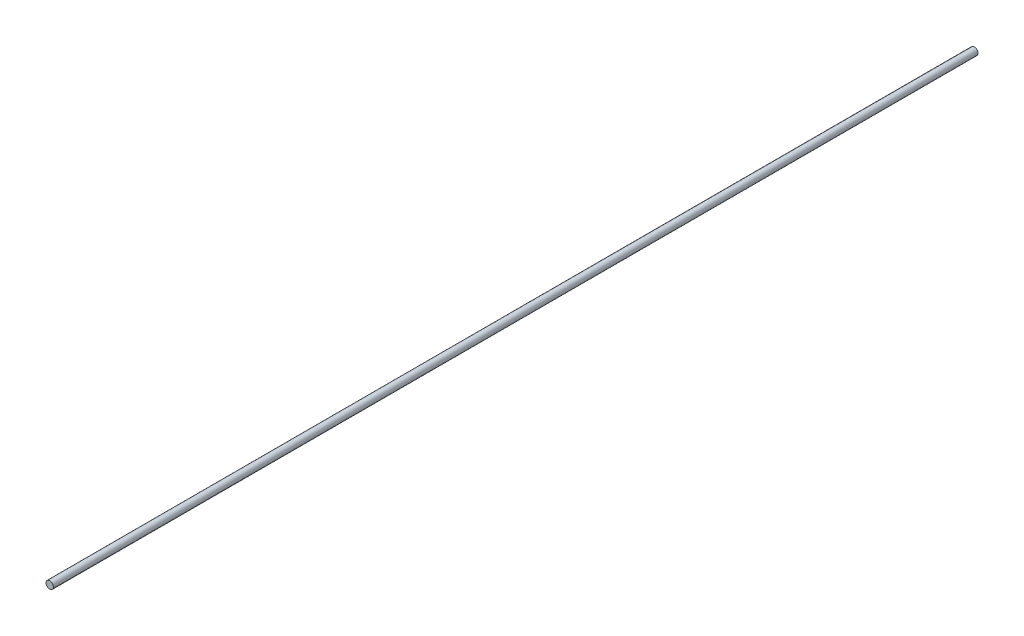
SolidWorks part; units mm, degrees
material "PLA Aero Bambu"
ref_plane "Front Plane" through (0, 0, 0) normal (0, 0, 1) x (1, 0, 0)
ref_plane "Top Plane" through (0, 0, 0) normal (0, 1, 0) x (1, 0, 0)
ref_plane "Right Plane" through (0, 0, 0) normal (1, 0, 0) x (0, 0, -1)
sketch "Sketch1" plane through (0, 0, 0) normal (0, 0, 1) x (1, 0, 0)
  circle A0 centre (0, 0) radius 0.975
  dimension "D1" = 1.95
extrude "Boss-Extrude1" add sketch "Sketch1" along normal blind 244.38
sketch "Sketch2" plane through (0, 0, 0) normal (0, 0, 1) x (1, 0, 0)
  line L1 (-0.5, 0.5) -> (0.5, 0.5)
  line L2 (-0.5, 0.5) -> (-0.5, -0.5)
  line L3 (-0.5, -0.5) -> (0.5, -0.5)
  line L4 (0.5, 0.5) -> (0.5, -0.5)
  line L5 (-0.5, 0.5) -> (0.5, -0.5) construction
  line L6 (-0.5, -0.5) -> (0.5, 0.5) construction
  point P0 (0, 0)
  dimension "D1" = 1
extrude "Cut-Extrude1" cut sketch "Sketch2" along normal blind 5
